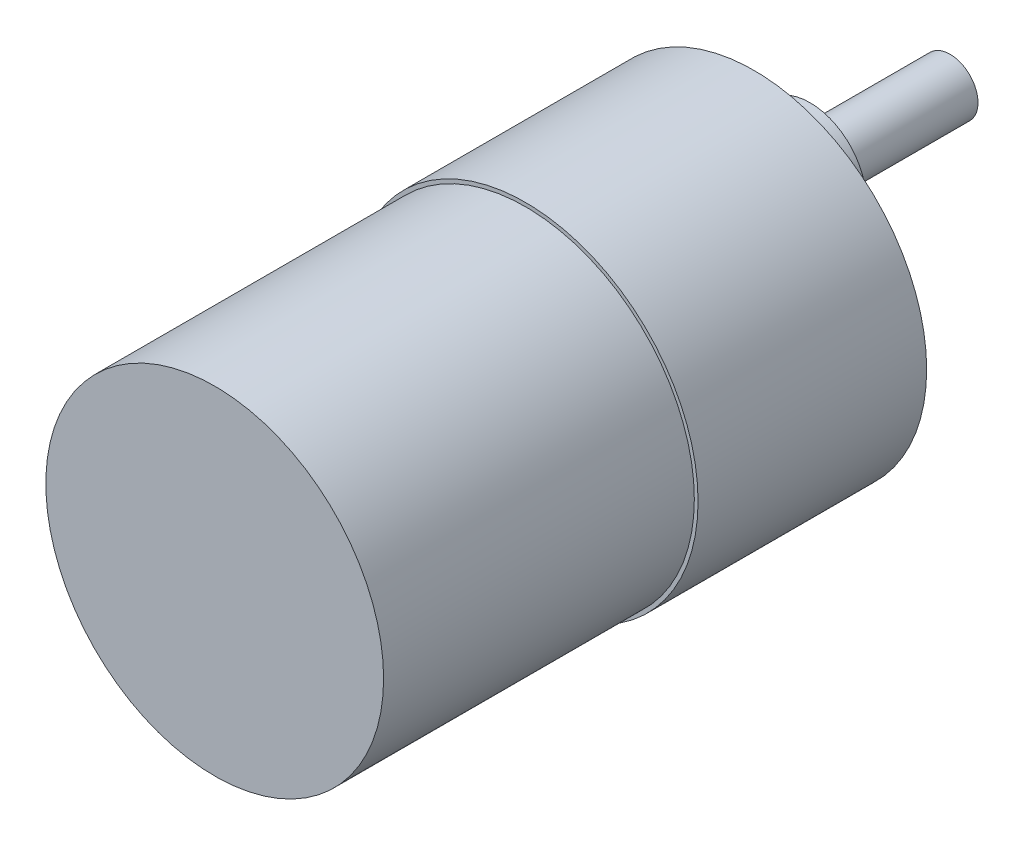
SolidWorks part; units mm, degrees
ref_plane "Front Plane" through (0, 0, 0) normal (0, 0, 1) x (1, 0, 0)
ref_plane "Top Plane" through (0, 0, 0) normal (0, 1, 0) x (1, 0, 0)
ref_plane "Right Plane" through (0, 0, 0) normal (1, 0, 0) x (0, 0, -1)
sketch "Sketch1" plane through (0, 0, 0) normal (0, 0, 1) x (1, 0, 0)
  circle A0 centre (0, 0) radius 18.5
extrude "Boss-Extrude1" add sketch "Sketch1" along normal blind 24.5
sketch "Sketch2" plane through (0, 0, 24.5) normal (0, 0, 1) x (1, 0, 0)
  circle A0 centre (0, 0) radius 18.1
extrude "Boss-Extrude2" add sketch "Sketch2" along normal blind 33.3
sketch "face diamentions" plane through (0, 0, 0) normal (0, 0, -1) x (-1, 0, 0)
  line L0 (0, 18.5) -> (0, 0.5) construction
  line L1 (0, 12.5) -> (0, 0.5) construction
  line L2 (0, 0) -> (-16, 0) construction
  line L3 (0, 0) -> (16, 0) construction
  line L4 (0, 0.5) -> (0, 6.5) construction
  circle A0 centre (0, 0) radius 18.5 construction
  circle A1 centre (0, 6.5) radius 6
  circle A2 centre (0, 6.5) radius 3
  circle A15 centre (-16, 0) radius 1.5
  circle A16 centre (8, 13.8564) radius 1.5
  circle A17 centre (8, -13.8564) radius 1.5
  circle A18 centre (16, 0) radius 1.5
  circle A19 centre (-8, -13.8564) radius 1.5
  circle A20 centre (-8, 13.8564) radius 1.5
  point P25 (0, 0)
  point P32 (0, 0)
  dimension "D1" = 3
  dimension "D2" = 16
  dimension "D3" = 3
sketch "Sketch4" plane through (0, 0, 0) normal (0, 0, -1) x (-1, 0, 0)
  circle A0 centre (0, 6.5) radius 6
extrude "Boss-Extrude3" add sketch "Sketch4" along normal blind 6
sketch "Sketch5" plane through (0, 0, -6) normal (0, 0, -1) x (-1, 0, 0)
  circle A0 centre (0, 6.5) radius 3
extrude "Boss-Extrude4" add sketch "Sketch5" along normal blind 15
sketch "Sketch6" plane through (0, 0, -21) normal (0, 0, -1) x (-1, 0, 0)
  line L0 (0, 6.5) -> (2.75, 6.5) construction
  line L1 (2.75, 6.5) -> (2.75, 5.301)
  line L2 (2.75, 6.5) -> (2.75, 7.699)
  arc A0 (2.75, 5.301) -> (2.75, 7.699) centre (0, 6.5) ccw
  dimension "D1" = 2.75
extrude "Cut-Extrude1" cut sketch "Sketch6" against normal blind 12
extrude "Cut-Extrude3" cut sketch "face diamentions" against normal blind 3 contours A18 | A15 | A16 | A17 | A19 | A20
